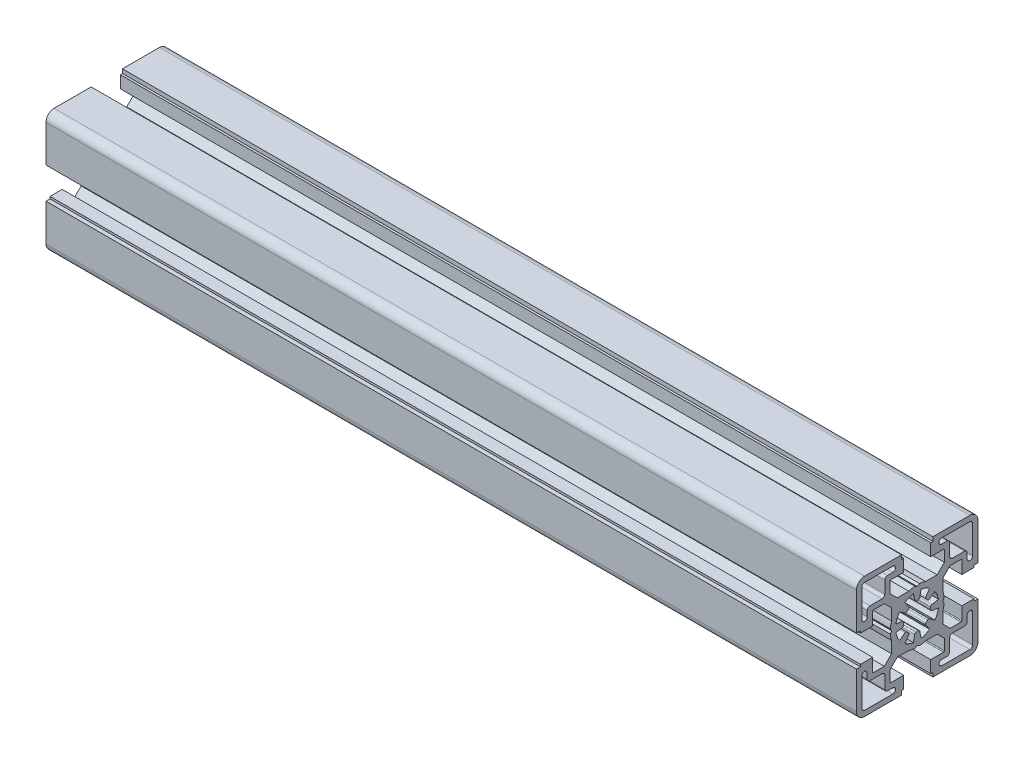
SolidWorks part; units mm, degrees
ref_plane "Спереди" through (0, 0, 0) normal (0, 0, 1) x (1, 0, 0)
ref_plane "Сверху" through (0, 0, 0) normal (0, 1, 0) x (1, 0, 0)
ref_plane "Справа" through (0, 0, 0) normal (1, 0, 0) x (0, 0, -1)
sketch "Эскиз2" plane through (0, 0, 0) normal (1, 0, 0) x (0, 0, -1)
  line L0 (-0.9511, 5.394) -> (-1.3892, 7.8785)
  line L1 (-3.1416, 4.4867) -> (-4.5886, 6.5532)
  line L2 (-4.4867, 3.1416) -> (-6.5532, 4.5886)
  line L3 (7.8785, -1.3892) -> (5.394, -0.9511)
  line L4 (-5.394, 0.9511) -> (-7.8785, 1.3892)
  line L5 (16.5, 5) -> (21, 5)
  line L6 (-21, 5) -> (-16.5, 5)
  line L7 (21, 5.8) -> (22.5, 5.8)
  line L8 (-22.5, 5.8) -> (-21, 5.8)
  line L9 (3.1225, 9.5) -> (7.3787, 9.5)
  line L10 (-7.3787, 9.5) -> (-3.1225, 9.5)
  line L11 (12.1713, 10.05) -> (16.2, 10.05)
  line L12 (-16.2, 10.05) -> (-12.1713, 10.05)
  line L13 (-17.5, 12) -> (-13, 12)
  line L14 (5, 16.5) -> (9.75, 16.5)
  line L15 (-9.75, 16.5) -> (-5, 16.5)
  line L16 (-19.5, 20.5) -> (-9, 20.5)
  line L17 (5, 21) -> (5.8, 21)
  line L18 (-5.8, 21) -> (-5, 21)
  line L19 (5.8, 22.5) -> (19.5, 22.5)
  line L20 (-19.5, 22.5) -> (-5.8, 22.5)
  line L21 (-7.8785, -1.3892) -> (-5.394, -0.9511)
  line L22 (5.394, 0.9511) -> (7.8785, 1.3892)
  line L23 (4.4867, 3.1416) -> (6.5532, 4.5886)
  line L24 (3.1416, 4.4867) -> (4.5886, 6.5532)
  line L25 (0.9511, 5.394) -> (1.3892, 7.8785)
  line L26 (-22.5, 5.8) -> (-22.5, 19.5)
  line L27 (-21, 5) -> (-21, 5.8)
  line L28 (-20.5, 9) -> (-20.5, 19.5)
  line L29 (-16.5, 5) -> (-16.5, 9.75)
  line L30 (-12, 13) -> (-12, 17.5)
  line L31 (-5.8, 21) -> (-5.8, 22.5)
  line L32 (-5, 16.5) -> (-5, 21)
  line L33 (5, 16.5) -> (5, 21)
  line L34 (5.8, 21) -> (5.8, 22.5)
  line L35 (9.5, 3.1225) -> (9.5, 7.3787)
  line L36 (10.05, 12.1713) -> (10.05, 16.2)
  line L37 (16.5, 5) -> (16.5, 9.75)
  line L38 (21, 5) -> (21, 5.8)
  line L39 (22.5, 5.8) -> (22.5, 19.5)
  line L40 (1.3892, -7.8785) -> (0.9511, -5.394)
  line L41 (4.5886, -6.5532) -> (3.1416, -4.4867)
  line L42 (6.5532, -4.5886) -> (4.4867, -3.1416)
  line L43 (-7.3787, -9.5) -> (-3.1225, -9.5)
  line L44 (3.1225, -9.5) -> (7.3787, -9.5)
  line L45 (-6.5532, -4.5886) -> (-4.4867, -3.1416)
  line L46 (-4.5886, -6.5532) -> (-3.1416, -4.4867)
  line L47 (-1.3892, -7.8785) -> (-0.9511, -5.394)
  line L48 (-9.5, -7.3787) -> (-9.5, -3.1225)
  line L49 (9.5, -7.3787) -> (9.5, -3.1225)
  line L50 (-22.5, -5.8) -> (-21, -5.8)
  line L51 (-21, -5) -> (-16.5, -5)
  line L52 (-21, -5.8) -> (-21, -5)
  line L53 (-16.5, -9.75) -> (-16.5, -5)
  line L54 (-22.5, -19.5) -> (-22.5, -5.8)
  line L55 (21, -5.8) -> (22.5, -5.8)
  line L56 (16.5, -5) -> (21, -5)
  line L57 (21, -5.8) -> (21, -5)
  line L58 (16.5, -9.75) -> (16.5, -5)
  line L59 (12.1713, -10.05) -> (16.2, -10.05)
  line L60 (22.5, -19.5) -> (22.5, -5.8)
  line L61 (-16.2, -10.05) -> (-12.1713, -10.05)
  line L62 (5, -16.5) -> (9.75, -16.5)
  line L63 (-9.75, -16.5) -> (-5, -16.5)
  line L64 (5, -21) -> (5.8, -21)
  line L65 (-5.8, -21) -> (-5, -21)
  line L66 (5.8, -22.5) -> (19.5, -22.5)
  line L67 (-19.5, -22.5) -> (-5.8, -22.5)
  line L68 (-10.05, -12.1713) -> (-10.05, -16.2)
  line L69 (-5.8, -21) -> (-5.8, -22.5)
  line L70 (-5, -16.5) -> (-5, -21)
  line L71 (5, -16.5) -> (5, -21)
  line L72 (5.8, -21) -> (5.8, -22.5)
  line L73 (10.05, -12.1713) -> (10.05, -16.2)
  line L74 (-9.5, 3.1225) -> (-9.5, 7.3787)
  line L75 (-9.5, 7.3787) -> (-12.1713, 10.05)
  line L76 (7.3787, 9.5) -> (10.05, 12.1713)
  line L77 (9.5, 7.3787) -> (12.1713, 10.05)
  line L78 (9.5, -7.3787) -> (12.1713, -10.05)
  line L79 (7.3787, -9.5) -> (10.05, -12.1713)
  line L80 (-7.3787, -9.5) -> (-10.05, -12.1713)
  line L81 (-12.1713, -10.05) -> (-9.5, -7.3787)
  line L82 (-10.05, 12.1713) -> (-10.05, 16.2)
  line L83 (-10.05, 12.1713) -> (-7.3787, 9.5)
  line L84 (-9.4624, 0) -> (-9.9624, 0.866)
  line L85 (-9.4624, 0) -> (-9.9624, -0.866)
  line L86 (0, -9.4624) -> (-0.866, -9.9624)
  line L87 (0, -9.4624) -> (0.866, -9.9624)
  line L88 (0, 9.4624) -> (0.866, 9.9624)
  line L89 (0, 9.4624) -> (-0.866, 9.9624)
  line L90 (9.4624, 0) -> (9.9624, -0.866)
  line L91 (9.4624, 0) -> (9.9624, 0.866)
  line L92 (-11, 18.5) -> (-9, 18.5)
  line L93 (-18.5, 11) -> (-18.5, 9)
  line L94 (17.5, 12) -> (13, 12)
  line L95 (12, 13) -> (12, 17.5)
  line L96 (19.5, 20.5) -> (9, 20.5)
  line L97 (11, 18.5) -> (9, 18.5)
  line L98 (20.5, 9) -> (20.5, 19.5)
  line L99 (18.5, 11) -> (18.5, 9)
  line L100 (-17.5, -12) -> (-13, -12)
  line L101 (-12, -13) -> (-12, -17.5)
  line L102 (-19.5, -20.5) -> (-9, -20.5)
  line L103 (-11, -18.5) -> (-9, -18.5)
  line L104 (-20.5, -9) -> (-20.5, -19.5)
  line L105 (-18.5, -11) -> (-18.5, -9)
  line L106 (19.5, -20.5) -> (9, -20.5)
  line L107 (11, -18.5) -> (9, -18.5)
  line L108 (17.5, -12) -> (13, -12)
  line L109 (12, -13) -> (12, -17.5)
  line L110 (20.5, -9) -> (20.5, -19.5)
  line L111 (18.5, -11) -> (18.5, -9)
  arc A0 (-19.5, 20.5) -> (-20.5, 19.5) centre (-19.5, 19.5) ccw
  arc A1 (-19.5, 22.5) -> (-22.5, 19.5) centre (-19.5, 19.5) ccw
  arc A2 (-13, 12) -> (-12, 13) centre (-13, 13) ccw
  arc A3 (-3.2283, 3.8181) -> (-3.8181, 3.2283) centre (0, 0) ccw
  arc A4 (3.8181, 3.2283) -> (3.2283, 3.8181) centre (0, 0) ccw
  arc A5 (-4.9826, 0.417) -> (-4.9826, -0.417) centre (0, 0) ccw
  arc A6 (0.417, 4.9826) -> (-0.417, 4.9826) centre (0, 0) ccw
  arc A7 (4.9826, -0.417) -> (4.9826, 0.417) centre (0, 0) ccw
  arc A8 (-6.5532, 4.5886) -> (-7.8785, 1.3892) centre (0, 0) ccw
  arc A9 (-1.3892, 7.8785) -> (-4.5886, 6.5532) centre (0, 0) ccw
  arc A10 (4.5886, 6.5532) -> (1.3892, 7.8785) centre (0, 0) ccw
  arc A11 (7.8785, 1.3892) -> (6.5532, 4.5886) centre (0, 0) ccw
  arc A12 (22.5, 19.5) -> (19.5, 22.5) centre (19.5, 19.5) ccw
  arc A13 (3.2283, -3.8181) -> (3.8181, -3.2283) centre (0, 0) ccw
  arc A14 (-3.8181, -3.2283) -> (-3.2283, -3.8181) centre (0, 0) ccw
  arc A15 (-0.417, -4.9826) -> (0.417, -4.9826) centre (0, 0) ccw
  arc A16 (6.5532, -4.5886) -> (7.8785, -1.3892) centre (0, 0) ccw
  arc A17 (1.3892, -7.8785) -> (4.5886, -6.5532) centre (0, 0) ccw
  arc A18 (-4.5886, -6.5532) -> (-1.3892, -7.8785) centre (0, 0) ccw
  arc A19 (-7.8785, -1.3892) -> (-6.5532, -4.5886) centre (0, 0) ccw
  arc A20 (-22.5, -19.5) -> (-19.5, -22.5) centre (-19.5, -19.5) ccw
  arc A21 (19.5, -22.5) -> (22.5, -19.5) centre (19.5, -19.5) ccw
  arc A22 (-4.4867, 3.1416) -> (-3.8181, 3.2283) centre (-4.1999, 3.5512) ccw
  arc A23 (-3.2283, 3.8181) -> (-3.1416, 4.4867) centre (-3.5512, 4.1999) ccw
  arc A24 (-0.9511, 5.394) -> (-0.417, 4.9826) centre (-0.4587, 5.4808) ccw
  arc A25 (0.417, 4.9826) -> (0.9511, 5.394) centre (0.4587, 5.4808) ccw
  arc A26 (3.1416, 4.4867) -> (3.2283, 3.8181) centre (3.5512, 4.1999) ccw
  arc A27 (3.8181, 3.2283) -> (4.4867, 3.1416) centre (4.1999, 3.5512) ccw
  arc A28 (5.394, 0.9511) -> (4.9826, 0.417) centre (5.4808, 0.4587) ccw
  arc A29 (4.9826, -0.417) -> (5.394, -0.9511) centre (5.4808, -0.4587) ccw
  arc A30 (4.4867, -3.1416) -> (3.8181, -3.2283) centre (4.1999, -3.5512) ccw
  arc A31 (3.2283, -3.8181) -> (3.1416, -4.4867) centre (3.5512, -4.1999) ccw
  arc A32 (0.9511, -5.394) -> (0.417, -4.9826) centre (0.4587, -5.4808) ccw
  arc A33 (-0.417, -4.9826) -> (-0.9511, -5.394) centre (-0.4587, -5.4808) ccw
  arc A34 (-3.1416, -4.4867) -> (-3.2283, -3.8181) centre (-3.5512, -4.1999) ccw
  arc A35 (-3.8181, -3.2283) -> (-4.4867, -3.1416) centre (-4.1999, -3.5512) ccw
  arc A36 (-5.394, -0.9511) -> (-4.9826, -0.417) centre (-5.4808, -0.4587) ccw
  arc A37 (-4.9826, 0.417) -> (-5.394, 0.9511) centre (-5.4808, 0.4587) ccw
  arc A38 (-16.5, -9.75) -> (-16.2, -10.05) centre (-16.2, -9.75) ccw
  arc A39 (-10.05, -16.2) -> (-9.75, -16.5) centre (-9.75, -16.2) ccw
  arc A40 (9.75, -16.5) -> (10.05, -16.2) centre (9.75, -16.2) ccw
  arc A41 (16.2, -10.05) -> (16.5, -9.75) centre (16.2, -9.75) ccw
  arc A42 (16.5, 9.75) -> (16.2, 10.05) centre (16.2, 9.75) ccw
  arc A43 (10.05, 16.2) -> (9.75, 16.5) centre (9.75, 16.2) ccw
  arc A44 (-9.75, 16.5) -> (-10.05, 16.2) centre (-9.75, 16.2) ccw
  arc A45 (-16.2, 10.05) -> (-16.5, 9.75) centre (-16.2, 9.75) ccw
  arc A46 (-9.9624, -0.866) -> (-9.5, -3.1225) centre (0, 0) ccw
  arc A47 (-9.5, 3.1225) -> (-9.9624, 0.866) centre (0, 0) ccw
  arc A48 (-3.1225, -9.5) -> (-0.866, -9.9624) centre (0, 0) ccw
  arc A49 (3.1225, 9.5) -> (0.866, 9.9624) centre (0, 0) ccw
  arc A50 (9.5, -3.1225) -> (9.9624, -0.866) centre (0, 0) ccw
  arc A51 (-0.866, 9.9624) -> (-3.1225, 9.5) centre (0, 0) ccw
  arc A52 (9.9624, 0.866) -> (9.5, 3.1225) centre (0, 0) ccw
  arc A53 (0.866, -9.9624) -> (3.1225, -9.5) centre (0, 0) ccw
  arc A54 (-11, 18.5) -> (-12, 17.5) centre (-11, 17.5) ccw
  arc A55 (-9, 18.5) -> (-9, 20.5) centre (-9, 19.5) ccw
  arc A56 (-17.5, 12) -> (-18.5, 11) centre (-17.5, 11) ccw
  arc A57 (-20.5, 9) -> (-18.5, 9) centre (-19.5, 9) ccw
  arc A58 (20.5, 19.5) -> (19.5, 20.5) centre (19.5, 19.5) ccw
  arc A59 (12, 13) -> (13, 12) centre (13, 13) ccw
  arc A60 (12, 17.5) -> (11, 18.5) centre (11, 17.5) ccw
  arc A61 (18.5, 11) -> (17.5, 12) centre (17.5, 11) ccw
  arc A62 (9, 20.5) -> (9, 18.5) centre (9, 19.5) ccw
  arc A63 (18.5, 9) -> (20.5, 9) centre (19.5, 9) ccw
  arc A64 (-20.5, -19.5) -> (-19.5, -20.5) centre (-19.5, -19.5) ccw
  arc A65 (-12, -13) -> (-13, -12) centre (-13, -13) ccw
  arc A66 (-12, -17.5) -> (-11, -18.5) centre (-11, -17.5) ccw
  arc A67 (-18.5, -11) -> (-17.5, -12) centre (-17.5, -11) ccw
  arc A68 (-9, -20.5) -> (-9, -18.5) centre (-9, -19.5) ccw
  arc A69 (-18.5, -9) -> (-20.5, -9) centre (-19.5, -9) ccw
  arc A70 (19.5, -20.5) -> (20.5, -19.5) centre (19.5, -19.5) ccw
  arc A71 (11, -18.5) -> (12, -17.5) centre (11, -17.5) ccw
  arc A72 (9, -18.5) -> (9, -20.5) centre (9, -19.5) ccw
  arc A73 (13, -12) -> (12, -13) centre (13, -13) ccw
  arc A74 (17.5, -12) -> (18.5, -11) centre (17.5, -11) ccw
  arc A75 (20.5, -9) -> (18.5, -9) centre (19.5, -9) ccw
extrude "Бобышка-Вытянуть1" add sketch "Эскиз2" along normal blind 300 contours L75 L12 A45 L29 L6 L27 L8 L26 A1 L20 L31 L18 L32 L15 A44 L82 L83 L10 A51 L89 L88 A49 L9 L76 L36 A43 L14 L33 L17 L34 L19 A12 L39 L7 L38 L5 L37 A42 L11 L77 L35 A52 L91 L90 A50 L49 L78 L59 A41 L58 L56 L57 L55 L60 A21 L66 L72 L64 L71 L62 A40 L73 L79 L44 A53 L87 L86 A48 L43 L80 L68 A39 L63 L70 L65 L69 L67 A20 L54 L50 L52 L51 L53 A38 L61 L81 L48 A46 L85 L84 A47 L74
sketch "Эскиз3" plane through (0, 0, 0) normal (-1, 0, 0) x (0, 0, 1)
  line L0 (-0.9511, 5.394) -> (-1.3892, 7.8785)
  line L1 (-3.1416, 4.4867) -> (-4.5886, 6.5532)
  line L2 (-4.4867, 3.1416) -> (-6.5532, 4.5886)
  line L3 (7.8785, -1.3892) -> (5.394, -0.9511)
  line L4 (-5.394, 0.9511) -> (-7.8785, 1.3892)
  line L13 (-17.5, 12) -> (-13, 12)
  line L16 (-19.5, 20.5) -> (-9, 20.5)
  line L21 (-7.8785, -1.3892) -> (-5.394, -0.9511)
  line L22 (5.394, 0.9511) -> (7.8785, 1.3892)
  line L23 (4.4867, 3.1416) -> (6.5532, 4.5886)
  line L24 (3.1416, 4.4867) -> (4.5886, 6.5532)
  line L25 (0.9511, 5.394) -> (1.3892, 7.8785)
  line L28 (-20.5, 9) -> (-20.5, 19.5)
  line L30 (-12, 13) -> (-12, 17.5)
  line L40 (1.3892, -7.8785) -> (0.9511, -5.394)
  line L41 (4.5886, -6.5532) -> (3.1416, -4.4867)
  line L42 (6.5532, -4.5886) -> (4.4867, -3.1416)
  line L45 (-6.5532, -4.5886) -> (-4.4867, -3.1416)
  line L46 (-4.5886, -6.5532) -> (-3.1416, -4.4867)
  line L47 (-1.3892, -7.8785) -> (-0.9511, -5.394)
  line L92 (-11, 18.5) -> (-9, 18.5)
  line L93 (-18.5, 11) -> (-18.5, 9)
  line L94 (17.5, 12) -> (13, 12)
  line L95 (12, 13) -> (12, 17.5)
  line L96 (19.5, 20.5) -> (9, 20.5)
  line L97 (11, 18.5) -> (9, 18.5)
  line L98 (20.5, 9) -> (20.5, 19.5)
  line L99 (18.5, 11) -> (18.5, 9)
  line L100 (-17.5, -12) -> (-13, -12)
  line L101 (-12, -13) -> (-12, -17.5)
  line L102 (-19.5, -20.5) -> (-9, -20.5)
  line L103 (-11, -18.5) -> (-9, -18.5)
  line L104 (-20.5, -9) -> (-20.5, -19.5)
  line L105 (-18.5, -11) -> (-18.5, -9)
  line L106 (19.5, -20.5) -> (9, -20.5)
  line L107 (11, -18.5) -> (9, -18.5)
  line L108 (17.5, -12) -> (13, -12)
  line L109 (12, -13) -> (12, -17.5)
  line L110 (20.5, -9) -> (20.5, -19.5)
  line L111 (18.5, -11) -> (18.5, -9)
  arc A0 (-19.5, 20.5) -> (-20.5, 19.5) centre (-19.5, 19.5) ccw
  arc A2 (-13, 12) -> (-12, 13) centre (-13, 13) ccw
  arc A3 (-3.2283, 3.8181) -> (-3.8181, 3.2283) centre (0, 0) ccw
  arc A4 (3.8181, 3.2283) -> (3.2283, 3.8181) centre (0, 0) ccw
  arc A5 (-4.9826, 0.417) -> (-4.9826, -0.417) centre (0, 0) ccw
  arc A6 (0.417, 4.9826) -> (-0.417, 4.9826) centre (0, 0) ccw
  arc A7 (4.9826, -0.417) -> (4.9826, 0.417) centre (0, 0) ccw
  arc A8 (-6.5532, 4.5886) -> (-7.8785, 1.3892) centre (0, 0) ccw
  arc A9 (-1.3892, 7.8785) -> (-4.5886, 6.5532) centre (0, 0) ccw
  arc A10 (4.5886, 6.5532) -> (1.3892, 7.8785) centre (0, 0) ccw
  arc A11 (7.8785, 1.3892) -> (6.5532, 4.5886) centre (0, 0) ccw
  arc A13 (3.2283, -3.8181) -> (3.8181, -3.2283) centre (0, 0) ccw
  arc A14 (-3.8181, -3.2283) -> (-3.2283, -3.8181) centre (0, 0) ccw
  arc A15 (-0.417, -4.9826) -> (0.417, -4.9826) centre (0, 0) ccw
  arc A16 (6.5532, -4.5886) -> (7.8785, -1.3892) centre (0, 0) ccw
  arc A17 (1.3892, -7.8785) -> (4.5886, -6.5532) centre (0, 0) ccw
  arc A18 (-4.5886, -6.5532) -> (-1.3892, -7.8785) centre (0, 0) ccw
  arc A19 (-7.8785, -1.3892) -> (-6.5532, -4.5886) centre (0, 0) ccw
  arc A22 (-4.4867, 3.1416) -> (-3.8181, 3.2283) centre (-4.1999, 3.5512) ccw
  arc A23 (-3.2283, 3.8181) -> (-3.1416, 4.4867) centre (-3.5512, 4.1999) ccw
  arc A24 (-0.9511, 5.394) -> (-0.417, 4.9826) centre (-0.4587, 5.4808) ccw
  arc A25 (0.417, 4.9826) -> (0.9511, 5.394) centre (0.4587, 5.4808) ccw
  arc A26 (3.1416, 4.4867) -> (3.2283, 3.8181) centre (3.5512, 4.1999) ccw
  arc A27 (3.8181, 3.2283) -> (4.4867, 3.1416) centre (4.1999, 3.5512) ccw
  arc A28 (5.394, 0.9511) -> (4.9826, 0.417) centre (5.4808, 0.4587) ccw
  arc A29 (4.9826, -0.417) -> (5.394, -0.9511) centre (5.4808, -0.4587) ccw
  arc A30 (4.4867, -3.1416) -> (3.8181, -3.2283) centre (4.1999, -3.5512) ccw
  arc A31 (3.2283, -3.8181) -> (3.1416, -4.4867) centre (3.5512, -4.1999) ccw
  arc A32 (0.9511, -5.394) -> (0.417, -4.9826) centre (0.4587, -5.4808) ccw
  arc A33 (-0.417, -4.9826) -> (-0.9511, -5.394) centre (-0.4587, -5.4808) ccw
  arc A34 (-3.1416, -4.4867) -> (-3.2283, -3.8181) centre (-3.5512, -4.1999) ccw
  arc A35 (-3.8181, -3.2283) -> (-4.4867, -3.1416) centre (-4.1999, -3.5512) ccw
  arc A36 (-5.394, -0.9511) -> (-4.9826, -0.417) centre (-5.4808, -0.4587) ccw
  arc A37 (-4.9826, 0.417) -> (-5.394, 0.9511) centre (-5.4808, 0.4587) ccw
  arc A54 (-11, 18.5) -> (-12, 17.5) centre (-11, 17.5) ccw
  arc A55 (-9, 18.5) -> (-9, 20.5) centre (-9, 19.5) ccw
  arc A56 (-17.5, 12) -> (-18.5, 11) centre (-17.5, 11) ccw
  arc A57 (-20.5, 9) -> (-18.5, 9) centre (-19.5, 9) ccw
  arc A58 (20.5, 19.5) -> (19.5, 20.5) centre (19.5, 19.5) ccw
  arc A59 (12, 13) -> (13, 12) centre (13, 13) ccw
  arc A60 (12, 17.5) -> (11, 18.5) centre (11, 17.5) ccw
  arc A61 (18.5, 11) -> (17.5, 12) centre (17.5, 11) ccw
  arc A62 (9, 20.5) -> (9, 18.5) centre (9, 19.5) ccw
  arc A63 (18.5, 9) -> (20.5, 9) centre (19.5, 9) ccw
  arc A64 (-20.5, -19.5) -> (-19.5, -20.5) centre (-19.5, -19.5) ccw
  arc A65 (-12, -13) -> (-13, -12) centre (-13, -13) ccw
  arc A66 (-12, -17.5) -> (-11, -18.5) centre (-11, -17.5) ccw
  arc A67 (-18.5, -11) -> (-17.5, -12) centre (-17.5, -11) ccw
  arc A68 (-9, -20.5) -> (-9, -18.5) centre (-9, -19.5) ccw
  arc A69 (-18.5, -9) -> (-20.5, -9) centre (-19.5, -9) ccw
  arc A70 (19.5, -20.5) -> (20.5, -19.5) centre (19.5, -19.5) ccw
  arc A71 (11, -18.5) -> (12, -17.5) centre (11, -17.5) ccw
  arc A72 (9, -18.5) -> (9, -20.5) centre (9, -19.5) ccw
  arc A73 (13, -12) -> (12, -13) centre (13, -13) ccw
  arc A74 (17.5, -12) -> (18.5, -11) centre (17.5, -11) ccw
  arc A75 (20.5, -9) -> (18.5, -9) centre (19.5, -9) ccw
extrude "Вырез-Вытянуть1" cut sketch "Эскиз3" against normal through all
